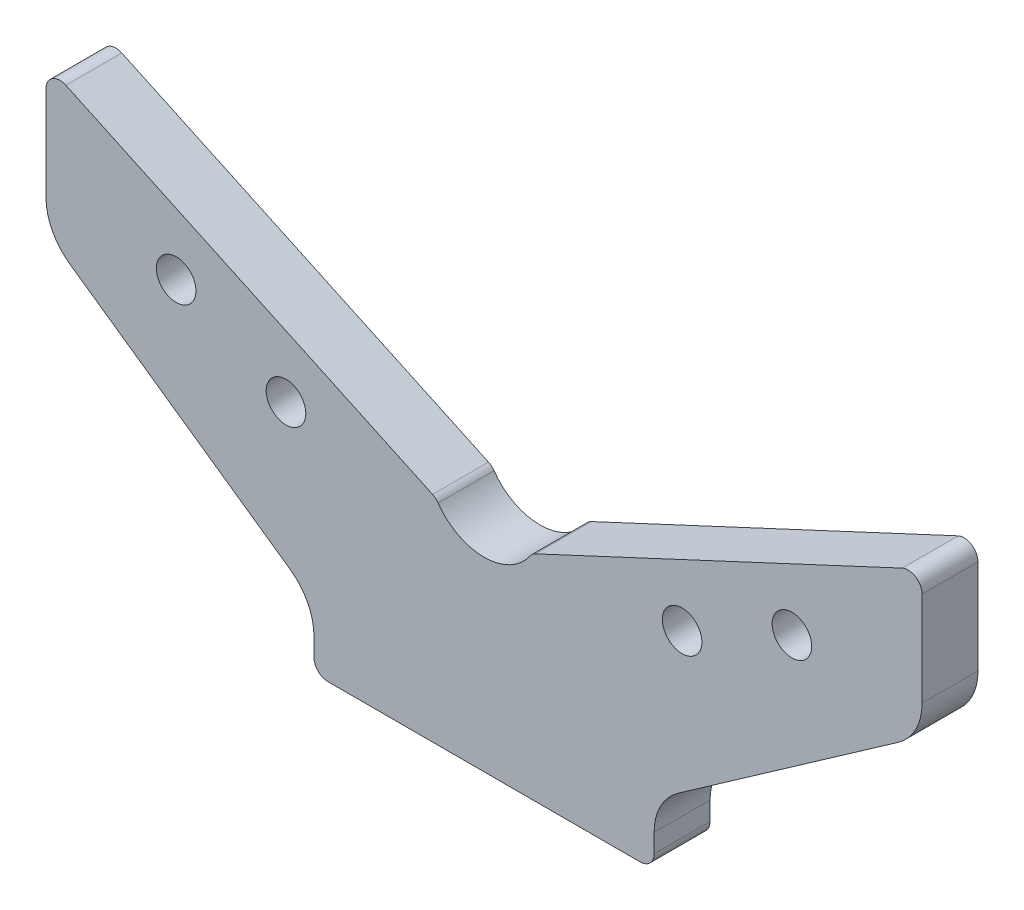
SolidWorks part; units mm, degrees
ref_plane "Front" through (0, 0, 0) normal (0, 0, 1) x (1, 0, 0)
ref_plane "Top" through (0, 0, 0) normal (0, 1, 0) x (1, 0, 0)
ref_plane "Right" through (0, 0, 0) normal (1, 0, 0) x (0, 0, -1)
sketch "Sketch1" plane through (0, 0, 0) normal (0, 0, 1) x (1, 0, 0)
  line L0 (36.5, 6.9913) -> (36.5, 3)
  line L1 (-36.5, 6.9913) -> (-36.5, 3)
  line L2 (0, 0) -> (33.5, 0)
  line L3 (0, 0) -> (-33.5, 0)
  line L4 (89.7321, 82.7189) -> (11.0434, 46.0258)
  line L5 (0, 0) -> (0, 40.8761) construction
  line L6 (-94, 59.7468) -> (-94, 80)
  line L7 (-89.7321, 82.7189) -> (-11.0434, 46.0258)
  line L8 (41.6171, 16.8211) -> (88.8829, 49.917)
  line L10 (94, 59.7468) -> (94, 80)
  line L11 (-41.6171, 16.8211) -> (-88.8829, 49.917)
  arc A0 (36.5, 6.9913) -> (41.6171, 16.8211) centre (48.5, 6.9913) cw
  arc A1 (-36.5, 6.9913) -> (-41.6171, 16.8211) centre (-48.5, 6.9913) ccw
  arc A2 (36.5, 3) -> (33.5, 0) centre (33.5, 3) cw
  arc A3 (89.7321, 82.7189) -> (94, 80) centre (91, 80) cw
  arc A4 (-94, 80) -> (-89.7321, 82.7189) centre (-91, 80) cw
  arc A5 (88.8829, 49.917) -> (94, 59.7468) centre (82, 59.7468) ccw
  arc A6 (-36.5, 3) -> (-33.5, 0) centre (-33.5, 3) ccw
  arc A9 (-88.8829, 49.917) -> (-94, 59.7468) centre (-82, 59.7468) cw
  arc A10 (-9.849, 45.0207) -> (9.849, 45.0207) centre (0, 51.8761) ccw
  arc A11 (-9.849, 45.0207) -> (-11.0434, 46.0258) centre (-12.3113, 43.3068) ccw
  arc A12 (9.849, 45.0207) -> (11.0434, 46.0258) centre (12.3113, 43.3068) cw
  point P15 (36.5, 0)
  point P19 (94, 84.7091)
  point P23 (-94, 84.7091)
  point P26 (94, 0)
  point P29 (-36.5, 0)
  point P32 (94, 53.5)
  point P43 (0, 40.8761)
  dimension "D5" = 29.5
  dimension "D6" = 3
  dimension "D7" = 12
  dimension "D8" = 3
  dimension "D13" = 12
  dimension "D15" = 12
  dimension "D16" = 3
  dimension "D2" = 73
  dimension "D3" = 65
  dimension "D4" = 25
  dimension "D9" = 188
  dimension "D10" = 83
  dimension "D11" = 55
  dimension "D12" = 40.8761
  dimension "D14" = 11
  dimension "D17" = 43.5753
extrude "Extrude1" add sketch "Sketch1" along normal blind 12
hole_wizard "M10 gevindhuller" positions "Sketch5" profile "Sketch4" legacy
sketch "Sketch5" plane through (0, 0, 12) normal (0, 0, 1) x (1, 0, 0)
  line L0 (0, 0) -> (0, 51.8761) construction
  line L1 (-42.5, 47.4537) -> (-66.064, 58.4418) construction
  line L2 (-11.0434, 46.0258) -> (-89.7321, 82.7189) construction
  point P0 (-66.064, 58.4418)
  point P6 (-42.5, 47.4537)
  point P10 (66.064, 58.4418)
  point P11 (42.5, 47.4537)
  dimension "D1" = 12
  dimension "D2" = 26
  dimension "D3" = 85
sketch "Sketch4" plane through (-66.064, 58.4418, 12) normal (1, 0, 0) x (0, -1, 0)
  line L0 (0, 0) -> (0, 24.5537)
  line L1 (0, 24.5537) -> (4.25, 22)
  line L2 (4.25, 22) -> (4.25, 0)
  line L4 (4.25, 0) -> (0, 0)
  line L6 (0, 24.5537) -> (-4.25, 22) construction
  line L7 (0, -4.2442) -> (0, 117.3081) construction
  dimension "Diameter" = 8.5
  dimension "Depth" = 22
  dimension "Drill Angle" = 118
cosmetic thread "Cosmetic Thread1" parameters "D1"=17, "D2"=10
cosmetic thread "Cosmetic Thread2" parameters "D1"=17, "D2"=10
cosmetic thread "Cosmetic Thread3" parameters "D1"=17, "D2"=10
cosmetic thread "Cosmetic Thread4" parameters "D1"=17, "D2"=10
